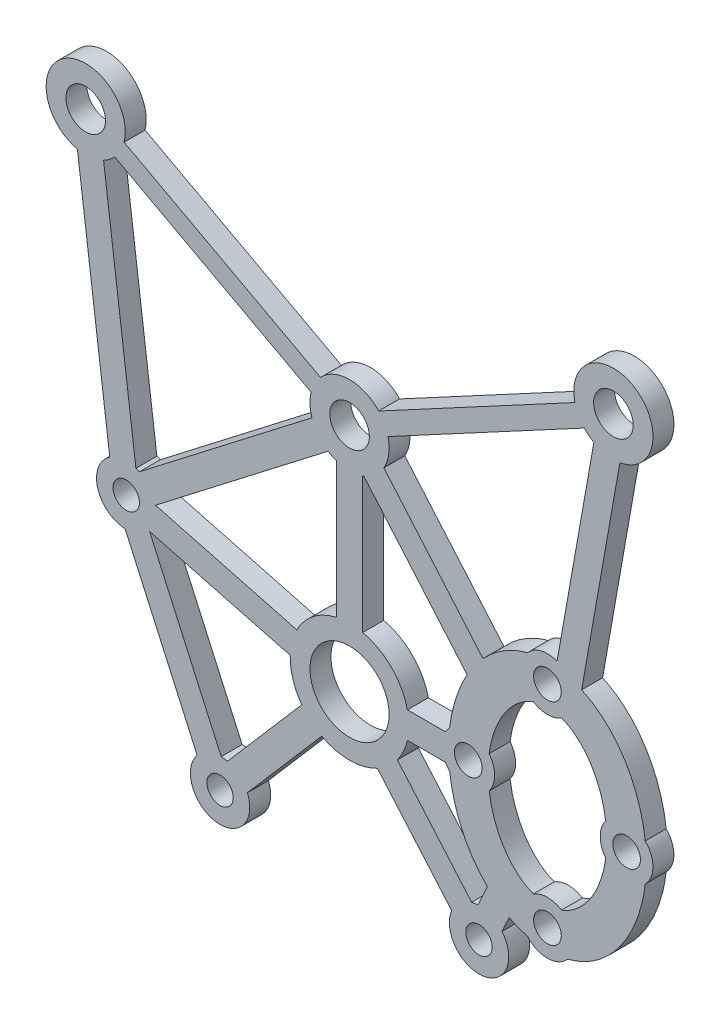
SolidWorks part; units mm, degrees
ref_plane "Front Plane" through (0, 0, 0) normal (0, 0, 1) x (1, 0, 0)
ref_plane "Top Plane" through (0, 0, 0) normal (0, 1, 0) x (1, 0, 0)
ref_plane "Right Plane" through (0, 0, 0) normal (1, 0, 0) x (0, 0, -1)
sketch "Sketch1" plane through (0, 0, 0) normal (0, 0, 1) x (1, 0, 0)
  line L0 (4, 72.0912) -> (4, -70.9088) construction
  line L1 (35, 64.3912) -> (-27, 64.3912) construction
  line L2 (-27, 64.3912) -> (-27, 14.3912) construction
  line L3 (-1011.6374, 14.3912) -> (48988.3626, 14.3912) construction
  line L4 (44, 14.3912) -> (-36, 14.3912) construction
  line L5 (4, 64.3912) -> (4, 72.0912) construction
  circle A0 centre (-36, 14.3912) radius 40 construction
  circle A1 centre (44, 14.3912) radius 40 construction
  circle A2 centre (-36, 14.3912) radius 48 construction
  circle A3 centre (-29.8555, -33.2139) radius 30 construction
  circle A4 centre (-29.8555, -33.2139) radius 35 construction
  circle A5 centre (4, -42.0912) radius 25 construction
  circle A6 centre (4, -42.0912) radius 30 construction
  circle A7 centre (34, -42.0912) radius 5 construction
  point P3 (4, -7.1088)
  point P6 (4, 64.3912)
  point P23 (4, 14.3912)
sketch "Sketch6" plane through (0, 0, 0) normal (0, 0, 1) x (1, 0, 0)
  line L0 (4, -13.1088) -> (4, -4.1088) construction
  line L1 (-78.6527, -26.4005) -> (-75.8339, -34.3198) construction
  line L3 (-27, 70.3912) -> (35, 70.3912) construction
  line L4 (-33, 64.3912) -> (-33, 38.6361) construction
  line L5 (-30, 38.6539) -> (-30, 56.6613) construction
  line L6 (-82.6206, -24.1989) -> (-78.6131, -35.4582) construction
  line L8 (-27, 58.3912) -> (2.5, 58.3912) construction
  line L9 (-78.6527, -26.4005) -> (-75.8339, -34.3198) construction
  line L10 (7, 68.3912) -> (7, 60.3912) construction
  line L11 (38, 38.6539) -> (38, 56.6613) construction
  line L12 (41, 64.3912) -> (41, 38.6361) construction
  line L14 (4, -71.398) -> (4, -68.398) construction
  line L15 (86.6527, -26.4005) -> (83.8339, -34.3198) construction
  line L16 (90.6206, -24.1989) -> (86.6131, -35.4582) construction
  line L17 (7, 60.3912) -> (29.225, 60.3347) construction
  line L18 (1, 68.3912) -> (-21.1857, 68.3912) construction
  line L19 (1, 60.3912) -> (-21.225, 60.3347) construction
  line L20 (1, 68.3912) -> (1, 60.3912) construction
  line L22 (7, 68.3912) -> (29.1857, 68.3912) construction
  line L23 (9.8273, -5.6796) -> (39.593, 10.3195) construction
  line L25 (8.407, -3.0371) -> (38.1727, 12.962) construction
  line L26 (-0.407, -3.0371) -> (-30.1727, 12.962) construction
  line L27 (-82.6206, -24.1989) -> (-78.6131, -35.4582) construction
  line L28 (-1.8273, -5.6796) -> (-31.593, 10.3195) construction
  line L29 (2.5, 58.3912) -> (2.5, -1.2993) construction
  line L30 (5.5, 58.3912) -> (5.5, -1.2993) construction
  line L31 (-20.3237, -69.3772) -> (-12.3101, -70.4607) construction
  line L33 (5.5, 58.3912) -> (35, 58.3912) construction
  line L34 (28.3237, -69.3772) -> (20.3101, -70.4607) construction
  circle A0 centre (-29.8555, -33.2139) radius 1.5 construction
  circle A1 centre (4, -42.0912) radius 3 construction
  circle A2 centre (-36, 14.3912) radius 3 construction
  arc A3 (41.906, 22.6217) -> (38, 38.6539) centre (71.2749, 38.2688) cw construction
  circle A4 centre (-27, 64.3912) radius 1.75 construction
  arc A5 (70.1125, -56.5381) -> (86.6131, -35.4582) centre (46.6112, -21.1442) ccw construction
  arc A6 (-78.6527, -26.4005) -> (-80.5251, -19.4547) centre (-76.978, -22.2237) ccw construction
  arc A7 (2.5, -1.2993) -> (-0.407, -3.0371) centre (4, -7.1088) ccw construction
  circle A8 centre (-15.6303, -64.8414) radius 1.75 construction
  arc A9 (-60.6385, -53.9149) -> (-75.8339, -34.3198) centre (-38.6112, -21.1442) cw construction
  arc A10 (-11.984, -67.4785) -> (-19.8461, -66.4154) centre (-15.6303, -64.8414) ccw construction
  arc A11 (-62.1125, -56.5381) -> (-20.3237, -69.3772) centre (4.9364, 87.2669) ccw construction
  arc A12 (35, 58.3912) -> (35.91, 58.4606) centre (35, 64.3912) ccw construction
  arc A13 (-27.91, 58.4606) -> (-27, 58.3912) centre (-27, 64.3912) ccw construction
  circle A14 centre (4, -7.1088) radius 3 construction
  arc A15 (-1.8273, -5.6796) -> (9.8273, -5.6796) centre (4, -7.1088) ccw construction
  arc A16 (-12.3101, -70.4607) -> (4, -71.398) centre (4.9364, 87.2669) ccw construction
  arc A18 (-60.6385, -53.9149) -> (-19.8461, -66.4154) centre (4.9369, 87.2668) ccw construction
  circle A19 centre (4, 64.3912) radius 1.5 construction
  arc A20 (-41.0308, 11.1215) -> (-31.593, 10.3195) centre (-36, 14.3912) ccw construction
  arc A21 (38, 56.6613) -> (35.91, 58.4606) centre (35.6377, 56.0308) ccw construction
  arc A22 (-82.6206, -24.1989) -> (-86.4255, 0.7974) centre (123.9884, 20.0379) cw construction
  arc A23 (-83.4406, 1.0998) -> (-79.978, 5.4611) centre (-79.5286, 1.5491) cw construction
  arc A24 (-11.984, -67.4785) -> (4, -68.398) centre (4.9369, 87.2668) ccw construction
  arc A25 (-27, 70.3912) -> (-33, 64.3912) centre (-27, 64.3912) ccw construction
  arc A26 (-33.906, 22.6217) -> (-33.0073, 19.5916) centre (-31.8394, 21.5863) ccw construction
  circle A27 centre (84.978, -22.2237) radius 1.75 construction
  arc A28 (63.3161, 7.2209) -> (51.6943, 11.6604) centre (67.4497, 35.4737) cw construction
  arc A29 (87.978, 5.4611) -> (63.3161, 7.2209) centre (100.9434, 360.8481) cw construction
  arc A30 (91.4406, 1.0998) -> (87.978, 5.4611) centre (87.5286, 1.5491) ccw construction
  arc A31 (88.5251, -19.4547) -> (91.4406, 1.0998) centre (-115.9884, 20.0379) ccw construction
  arc A33 (48.1542, 18.7204) -> (41, 38.6361) centre (71.2749, 38.2688) cw construction
  arc A34 (51.6943, 11.6604) -> (49.0308, 11.1215) centre (50.632, 10.0592) ccw construction
  arc A35 (41, 64.3912) -> (35, 70.3912) centre (35, 64.3912) ccw construction
  arc A36 (-86.4255, 0.7974) -> (-80.1875, 8.4555) centre (-79.5286, 1.5491) cw construction
  circle A37 centre (-76.978, -22.2237) radius 1.75 construction
  arc A38 (63.6936, 10.1977) -> (48.1542, 18.7204) centre (67.4497, 35.4737) cw construction
  arc A39 (88.1875, 8.4555) -> (63.6936, 10.1977) centre (100.9434, 360.8481) cw construction
  arc A40 (94.4255, 0.7974) -> (88.1875, 8.4555) centre (87.5286, 1.5491) ccw construction
  arc A41 (19.984, -67.4785) -> (4, -68.398) centre (3.0631, 87.2668) cw construction
  arc A42 (88.5251, -19.4547) -> (86.6527, -26.4005) centre (84.978, -22.2237) ccw construction
  arc A43 (-80.1875, 8.4555) -> (-55.6936, 10.1977) centre (-92.9434, 360.8481) ccw construction
  arc A44 (-55.6936, 10.1977) -> (-40.1542, 18.7204) centre (-59.4497, 35.4737) ccw construction
  arc A45 (-82.6206, -24.1989) -> (-86.4255, 0.7974) centre (123.9884, 20.0379) cw construction
  arc A46 (-43.6943, 11.6604) -> (-41.0308, 11.1215) centre (-42.632, 10.0592) cw construction
  arc A47 (-40.1542, 18.7204) -> (-33, 38.6361) centre (-63.2749, 38.2688) ccw construction
  arc A48 (68.6385, -53.9149) -> (27.8461, -66.4154) centre (3.0631, 87.2668) cw construction
  arc A49 (-80.5251, -19.4547) -> (-83.4406, 1.0998) centre (123.9884, 20.0379) cw construction
  arc A50 (-62.1125, -56.5381) -> (-78.6131, -35.4582) centre (-38.6112, -21.1442) cw construction
  arc A51 (-79.978, 5.4611) -> (-55.3161, 7.2209) centre (-92.9434, 360.8481) ccw construction
  arc A52 (-55.3161, 7.2209) -> (-43.6943, 11.6604) centre (-59.4497, 35.4737) ccw construction
  arc A54 (20.3101, -70.4607) -> (4, -71.398) centre (3.0636, 87.2669) cw construction
  arc A55 (-30, 56.6613) -> (-27.91, 58.4606) centre (-27.6377, 56.0308) cw construction
  arc A56 (70.1125, -56.5381) -> (28.3237, -69.3772) centre (3.0636, 87.2669) cw construction
  arc A57 (-30.1727, 12.962) -> (-33.0073, 19.5916) centre (-36, 14.3912) ccw construction
  arc A58 (41.906, 22.6217) -> (40.9857, 19.5791) centre (39.8394, 21.5863) cw construction
  arc A59 (19.984, -67.4785) -> (27.8461, -66.4154) centre (23.6303, -64.8414) cw construction
  arc A60 (68.6385, -53.9149) -> (83.8339, -34.3198) centre (46.6112, -21.1442) ccw construction
  circle A61 centre (23.6303, -64.8414) radius 1.75 construction
  arc A65 (90.6206, -24.1989) -> (94.4255, 0.7974) centre (-115.9884, 20.0379) ccw construction
  arc A66 (49.0308, 11.1215) -> (39.593, 10.3195) centre (44, 14.3912) cw construction
  circle A72 centre (35, 64.3912) radius 1.75 construction
  circle A73 centre (44, 14.3912) radius 3 construction
  arc A74 (-33.906, 22.6217) -> (-30, 38.6539) centre (-63.2749, 38.2688) ccw construction
  arc A75 (-21.1857, 68.3912) -> (-21.225, 60.3347) centre (-27, 64.3912) cw construction
  arc A77 (29.1857, 68.3912) -> (29.225, 60.3347) centre (35, 64.3912) ccw construction
  arc A78 (8.407, -3.0371) -> (5.5, -1.2993) centre (4, -7.1088) ccw construction
  arc A79 (38.1727, 12.962) -> (41.0073, 19.5916) centre (44, 14.3912) cw construction
  point P16 (4, -22.2237)
  point P44 (4, 9.0912)
  point P114 (4, 68.8177)
sketch "Sketch8" plane through (0, 0, 0) normal (0, 0, 1) x (1, 0, 0)
  line L0 (-13.0864, -14.5646) -> (1.7965, -22.5642)
  line L1 (-13.7965, -15.8858) -> (1.0864, -23.8854)
  line L2 (6.2035, -22.5642) -> (21.0864, -14.5646)
  line L3 (6.9136, -23.8854) -> (21.7965, -15.8858)
  line L5 (14.1169, -34.861) -> (6.6003, -26.0961)
  line L6 (-14.6462, -16.5271) -> (-12.194, -35.5256)
  line L7 (11.2679, -41.0912) -> (8.3875, -41.0912)
  line L8 (11.2679, -43.0912) -> (8.3875, -43.0912)
  line L9 (16.1016, -50.8612) -> (15.5611, -52.047)
  line L10 (14.4503, -49.6618) -> (13.7412, -51.2175)
  line L11 (-10.7052, -37.2015) -> (0, -40.0297)
  line L13 (24.4916, -16.8094) -> (21.5946, -33.1722)
  line L16 (12.9111, -36.5272) -> (5.0822, -27.398)
  line L17 (22.5222, -16.4608) -> (19.7304, -32.2294)
  line L18 (1.8908, -46.0663) -> (-3.7413, -52.5936)
  line L19 (13.2555, -51.287) -> (7.6234, -44.7597)
  line L21 (-5.7299, -51.2179) -> (-11.1575, -39.1505)
  line L22 (-11.1575, -39.1505) -> (-0.4978, -41.9509)
  line L27 (11.7413, -52.5936) -> (6.1092, -46.0663)
  line L29 (-7.5539, -52.0383) -> (-13.013, -39.9009)
  line L32 (2.3707, -27.119) -> (-10.7052, -37.2015)
  line L34 (1.1495, -25.5352) -> (-11.9422, -35.6299)
  line L42 (-16.6297, -16.7832) -> (-14.1775, -35.7816)
  line L47 (0.3766, -44.7597) -> (-5.2555, -51.287)
  line L53 (3, -37.7037) -> (3, -27.4284)
  line L54 (5, -37.7037) -> (5, -27.4284)
  circle A0 centre (-12.9277, -37.6525) radius 1
  arc A1 (7.6234, -44.7597) -> (8.3875, -43.0912) centre (4, -42.0912) ccw
  circle A2 centre (-16, -13.85) radius 1.5
  circle A3 centre (19, -42.0912) radius 6 construction
  circle A4 centre (19, -42.0912) radius 8 construction
  circle A5 centre (4, -42.0912) radius 3
  circle A6 centre (4, -24.6) radius 1.5
  circle A7 centre (19, -34.0912) radius 1.05
  circle A8 centre (25, -42.0912) radius 1.05
  arc A9 (2.3707, -27.119) -> (3, -27.4284) centre (4, -24.6) ccw
  arc A10 (-13.0864, -14.5646) -> (-16.6297, -16.7832) centre (-16, -13.85) ccw
  circle A11 centre (24, -13.85) radius 1.5
  circle A12 centre (19, -50.0912) radius 1.05
  circle A13 centre (13, -42.0912) radius 1.05
  arc A14 (21.7965, -15.8858) -> (22.5222, -16.4608) centre (24, -13.85) ccw
  arc A15 (-14.1775, -35.7816) -> (-13.013, -39.9009) centre (-12.9277, -37.6525) ccw
  circle A16 centre (13.8152, -53.4663) radius 1
  arc A17 (11.7413, -52.5936) -> (15.5611, -52.047) centre (13.8152, -53.4663) ccw
  circle A18 centre (-5.8152, -53.4663) radius 1
  arc A19 (-5.2555, -51.287) -> (-5.7299, -51.2179) centre (-5.8152, -53.4663) ccw
  arc A20 (6.6003, -26.0961) -> (6.9136, -23.8854) centre (4, -24.6) ccw
  arc A21 (5, -27.4284) -> (5.0822, -27.398) centre (4, -24.6) ccw
  arc A22 (1.0864, -23.8854) -> (1.1495, -25.5352) centre (4, -24.6) ccw
  arc A23 (6.2035, -22.5642) -> (1.7965, -22.5642) centre (4, -24.6) ccw
  arc A24 (-14.6462, -16.5271) -> (-13.7965, -15.8858) centre (-16, -13.85) ccw
  arc A25 (13.7412, -51.2175) -> (13.2555, -51.287) centre (13.8152, -53.4663) ccw
  arc A26 (8.3875, -41.0912) -> (5, -37.7037) centre (4, -42.0912) ccw
  arc A27 (-0.4978, -41.9509) -> (0.3766, -44.7597) centre (4, -42.0912) ccw
  arc A28 (1.8908, -46.0663) -> (6.1092, -46.0663) centre (4, -42.0912) ccw
  arc A29 (3, -37.7037) -> (0, -40.0297) centre (4, -42.0912) ccw
  arc A30 (-7.5539, -52.0383) -> (-3.7413, -52.5936) centre (-5.8152, -53.4663) ccw
  arc A31 (-11.9422, -35.6299) -> (-12.194, -35.5256) centre (-12.9277, -37.6525) ccw
  arc A32 (24.4916, -16.8094) -> (21.0864, -14.5646) centre (24, -13.85) ccw
  arc A33 (17.9319, -35.7821) -> (20.0681, -35.7821) centre (19, -34.0912) ccw
  arc A34 (11.5841, -40.6787) -> (11.2679, -41.0912) centre (13, -42.0912) ccw
  arc A35 (26.4159, -43.5037) -> (26.4159, -40.6787) centre (25, -42.0912) ccw
  arc A36 (17.4833, -51.3949) -> (20.5167, -51.3949) centre (19, -50.0912) ccw
  arc A37 (14.5828, -43.3138) -> (14.5828, -40.8686) centre (13, -42.0912) ccw
  arc A38 (11.2679, -43.0912) -> (11.5841, -43.5037) centre (13, -42.0912) ccw
  arc A39 (20.0681, -48.4003) -> (17.9319, -48.4003) centre (19, -50.0912) ccw
  arc A40 (23.4172, -40.8686) -> (23.4172, -43.3138) centre (25, -42.0912) ccw
  arc A41 (19.7304, -32.2294) -> (17.4833, -32.7875) centre (19, -34.0912) ccw
  spline S0 degree 3 poles (12.9111, -36.5272) (12.2117, -37.7658) (11.7605, -39.1989) (11.5841, -40.6787) knots 4.064937 4.064937 4.064937 4.064937 4.556896 4.556896 4.556896 4.556896
  spline S1 degree 3 poles (17.4833, -32.7875) (16.9625, -32.9225) (15.7273, -33.4158) (14.6659, -34.2664) (14.1169, -34.861) knots 3.333334 3.333334 3.333334 3.333334 3.534292 3.823411 3.823411 3.823411 3.823411
  spline S2 degree 3 poles (11.5841, -43.5037) (11.8099, -45.3984) (12.6588, -47.68) (14.1289, -49.3526) (14.4503, -49.6618) knots 4.867882 4.867882 4.867882 4.867882 5.497787 5.658332 5.658332 5.658332 5.658332
  spline S3 degree 3 poles (14.5828, -43.3138) (14.648, -43.794) (14.9404, -45.1251) (15.888, -46.9934) (17.0749, -48.0234) (17.7637, -48.3388) (17.9319, -48.4003) knots 4.89141 4.89141 4.89141 4.89141 5.105088 5.497787 5.890486 6.016864 6.016864 6.016864 6.016864
  spline S4 degree 3 poles (16.1016, -50.8612) (16.5426, -51.0917) (17.007, -51.2714) (17.4833, -51.3949) knots 5.907641 5.907641 5.907641 5.907641 6.091444 6.091444 6.091444 6.091444
  spline S5 degree 3 poles (20.0681, -48.4003) (20.2363, -48.3388) (20.9251, -48.0234) (22.112, -46.9934) (23.0596, -45.1251) (23.352, -43.794) (23.4172, -43.3138) knots 6.549507 6.549507 6.549507 6.549507 6.675884 7.068583 7.461283 7.67496 7.67496 7.67496 7.67496
  spline S6 degree 3 poles (20.5167, -51.3949) (21.0375, -51.2599) (22.5338, -50.6624) (25.0919, -48.3501) (26.1901, -45.3984) (26.4159, -43.5037) knots 6.474926 6.474926 6.474926 6.474926 6.675884 7.068583 7.698488 7.698488 7.698488 7.698488
  spline S7 degree 3 poles (23.4172, -40.8686) (23.352, -40.3884) (23.0596, -39.0573) (22.112, -37.189) (20.9251, -36.159) (20.2363, -35.8436) (20.0681, -35.7821) knots 8.033003 8.033003 8.033003 8.033003 8.246681 8.63938 9.032079 9.158456 9.158456 9.158456 9.158456
  spline S8 degree 3 poles (26.4159, -40.6787) (26.1901, -38.784) (25.0919, -35.8323) (22.8309, -33.7885) (21.7391, -33.2385) (21.5946, -33.1722) knots 8.009475 8.009475 8.009475 8.009475 8.63938 9.032079 9.090955 9.090955 9.090955 9.090955
  spline S9 degree 3 poles (17.9319, -35.7821) (17.7637, -35.8436) (17.0749, -36.159) (15.888, -37.189) (14.9404, -39.0573) (14.648, -40.3884) (14.5828, -40.8686) knots 9.6911 9.6911 9.6911 9.6911 9.817477 10.210176 10.602875 10.816553 10.816553 10.816553 10.816553
  point P53 (19, -42.0912)
extrude "Boss-Extrude1" add sketch "Sketch8" along normal blind 1.5875
